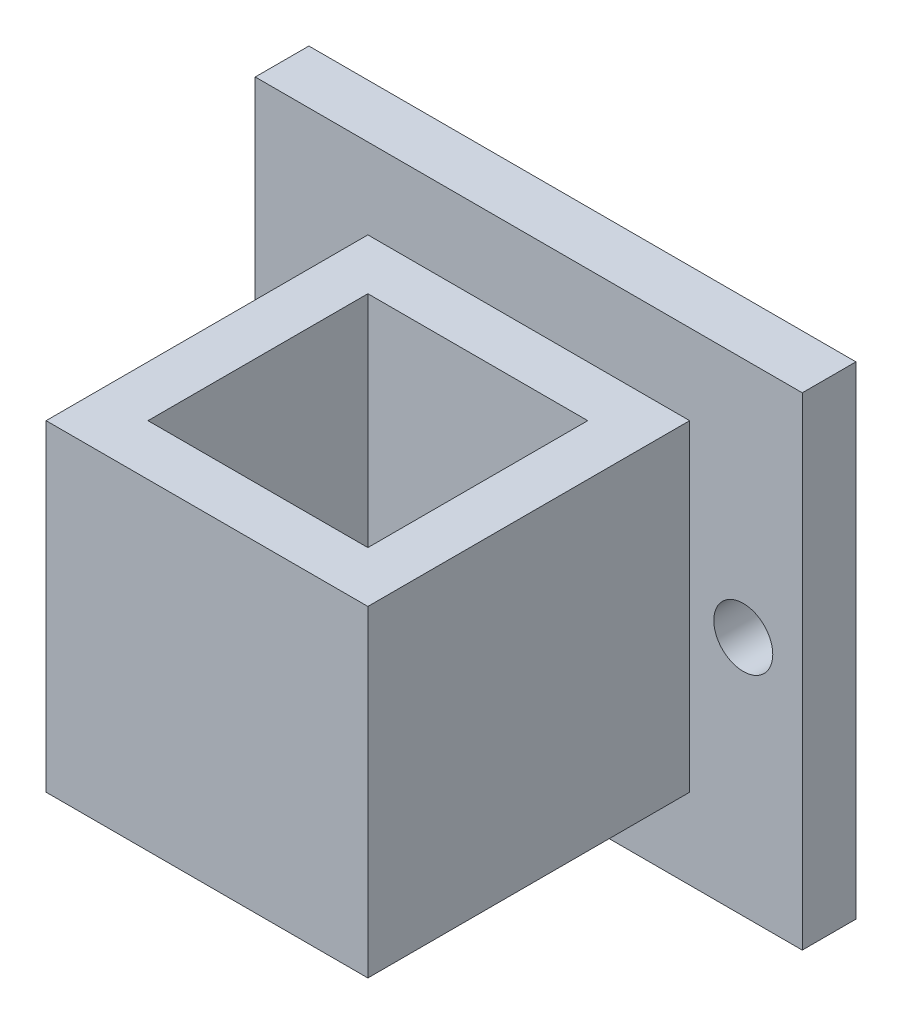
SolidWorks part; units mm, degrees
ref_plane "Front Plane" through (0, 0, 0) normal (0, 0, 1) x (1, 0, 0)
ref_plane "Top Plane" through (0, 0, 0) normal (0, 1, 0) x (1, 0, 0)
ref_plane "Right Plane" through (0, 0, 0) normal (1, 0, 0) x (0, 0, -1)
sketch "Sketch1" plane through (0, 0, 0) normal (0, 0, 1) x (1, 0, 0)
  line L0 (-25.5, -9.6794) -> (-25.5, -45.3206) construction
  line L1 (25.5, -60) -> (-25.5, -60)
  line L2 (25.5, -60) -> (25.5, -15)
  line L3 (25.5, -15) -> (-25.5, -15)
  line L4 (-25.5, -60) -> (-25.5, -15)
  line L5 (25.5, 5) -> (25.5, -60) construction
  line L6 (14.5, -60) -> (25.5, -60) construction
  line L7 (20, -37.5) -> (20, -60) construction
  line L8 (20, -37.5) -> (20, -15) construction
extrude "Boss-Extrude1" add sketch "Sketch1" along normal blind 5
sketch "Sketch2" plane through (0, 0, 5) normal (0, 0, 1) x (1, 0, 0)
  line L0 (-25.5, -15) -> (25.5, -60) construction
  line L1 (-10, -27.5) -> (10, -27.5) construction
  line L2 (-10, -27.5) -> (-10, -47.5) construction
  line L3 (-10, -47.5) -> (10, -47.5) construction
  line L4 (10, -27.5) -> (10, -47.5) construction
  line L5 (10, -27.5) -> (-10, -47.5) construction
  line L6 (-15, -22.5) -> (15, -22.5)
  line L7 (15, -22.5) -> (15, -52.5)
  line L8 (-15, -52.5) -> (15, -52.5)
  line L9 (-15, -22.5) -> (-15, -52.5)
  point P8 (0, -37.5)
  point P9 (0, -37.5)
  dimension "D1" = 20
  dimension "D2" = 20
  dimension "D3" = 5
extrude "Boss-Extrude2" add sketch "Sketch2" along normal blind 30
sketch "Sketch3" plane through (0, -52.5, 0) normal (0, -1, 0) x (1, 0, 0)
  line L0 (-10, 30) -> (10, 10) construction
  line L1 (-10, 30) -> (10, 30) construction
  line L2 (-10, 30) -> (-10, 10) construction
  line L3 (-10, 10) -> (10, 10) construction
  line L4 (10, 30) -> (10, 10) construction
  line L5 (15, 35) -> (-15, 5) construction
  line L6 (-10.25, 30.25) -> (10.25, 30.25)
  line L7 (10.25, 30.25) -> (10.25, 9.75)
  line L8 (-10.25, 9.75) -> (10.25, 9.75)
  line L9 (-10.25, 30.25) -> (-10.25, 9.75)
  point P8 (0, 20)
  point P9 (0, 20)
  dimension "D1" = 20
  dimension "D2" = 20
  dimension "D3" = 0.25
extrude "Cut-Extrude1" cut sketch "Sketch3" against normal through all
sketch "Sketch4" plane through (0, 0, 0) normal (0, 0, -1) x (-1, 0, 0)
  circle A0 centre (20, -37.5) radius 2.75
  circle A1 centre (-20, -37.5) radius 2.75
  dimension "D1" = 5.5
  dimension "D2" = 5.5
extrude "Cut-Extrude2" cut sketch "Sketch4" against normal through all
